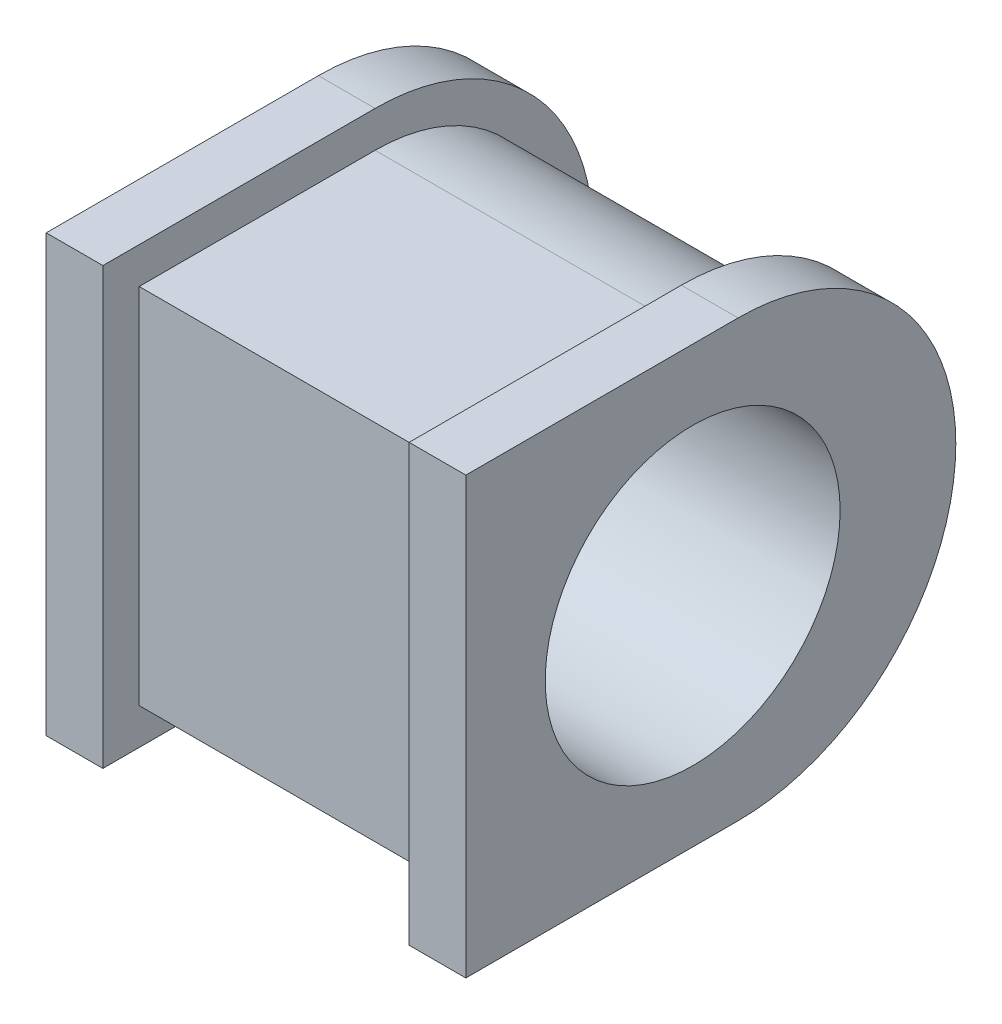
SolidWorks part; units mm, degrees
ref_plane "Front Plane" through (0, 0, 0) normal (0, 0, 1) x (1, 0, 0)
ref_plane "Top Plane" through (0, 0, 0) normal (0, 1, 0) x (1, 0, 0)
ref_plane "Right Plane" through (0, 0, 0) normal (1, 0, 0) x (0, 0, -1)
sketch "Sketch1" plane through (0, 0, 0) normal (1, 0, 0) x (0, 0, -1)
  line L1 (0, 0) -> (52, 0)
  line L2 (0, 0) -> (0, 80)
  line L3 (0, 80) -> (52, 80)
  arc A0 (52, 0) -> (52, 80) centre (52, 40) ccw
  dimension "D2" = 52
  dimension "D1" = 80
extrude "Boss-Extrude1" add sketch "Sketch1" along normal blind 80
sketch "Sketch2" plane through (80, 0, 0) normal (1, 0, 0) x (0, 0, -1)
  line L0 (-8, 88) -> (-8, -8)
  line L1 (-8, 88) -> (52, 88)
  line L2 (-8, -8) -> (52, -8)
  arc A0 (52, -8) -> (52, 88) centre (52, 40) ccw
  dimension "D1" = 48
  dimension "D2" = 60
extrude "Boss-Extrude2" add sketch "Sketch2" along normal blind 12.5
ref_plane "Plane1" through (46.25, 0, 0) normal (1, 0, 0) x (0, 0, -1)
mirror "Mirror1" about plane through (46.25, 0, 0) normal (1, 0, 0) of "Boss-Extrude2"
sketch "Sketch3" plane through (92.5, 0, 0) normal (1, 0, 0) x (0, 0, -1)
  line L0 (-8, 88) -> (-8, -8) construction
  circle A0 centre (42, 40) radius 32.5
  arc A1 (52, -8) -> (52, 88) centre (52, 40) ccw construction
  point P4 (0, 0)
  point P8 (100, 40)
  dimension "D1" = 50
  dimension "D2" = 65
extrude "Cut-Extrude1" cut sketch "Sketch3" against normal up to next
